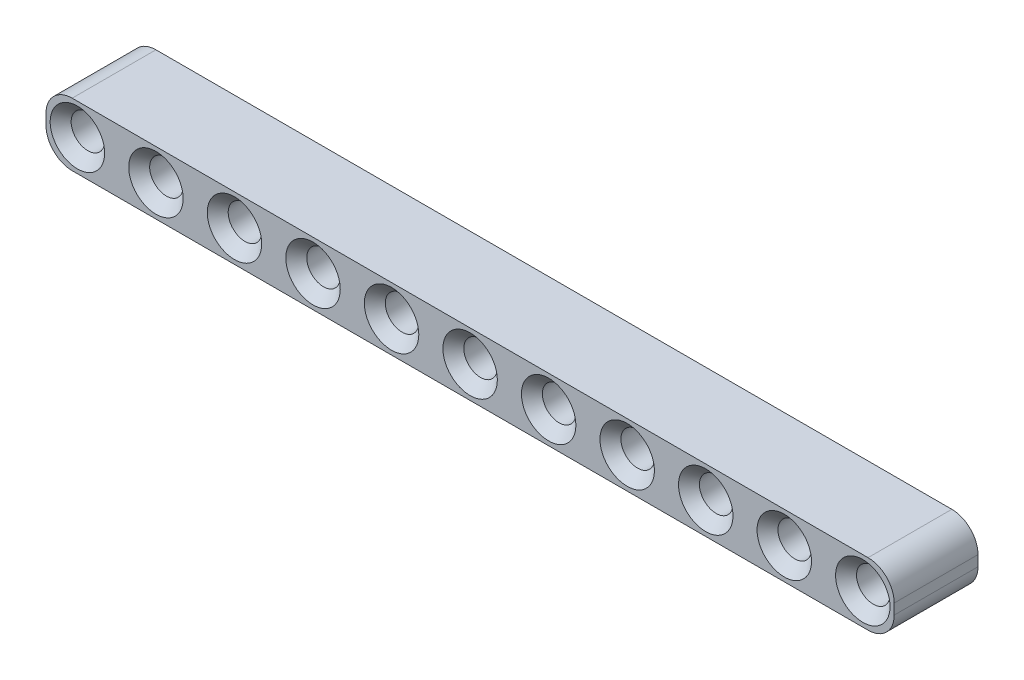
SolidWorks part; units mm, degrees
ref_plane "Front Plane" through (0, 0, 0) normal (0, 0, 1) x (1, 0, 0)
ref_plane "Top Plane" through (0, 0, 0) normal (0, 1, 0) x (1, 0, 0)
ref_plane "Right Plane" through (0, 0, 0) normal (1, 0, 0) x (0, 0, -1)
sketch "Sketch1" plane through (0, 0, 0) normal (0, 0, 1) x (1, 0, 0)
  line L1 (-0.5, 3) -> (75.5, 3)
  line L2 (-3, 0.5) -> (-3, -0.5)
  line L3 (-0.5, -3) -> (75.5, -3)
  line L4 (78, 0.5) -> (78, -0.5)
  circle A0 centre (0, 0) radius 1.6
  arc A1 (75.5, -3) -> (78, -0.5) centre (75.5, -0.5) ccw
  arc A2 (75.5, 3) -> (78, 0.5) centre (75.5, 0.5) cw
  arc A3 (-3, -0.5) -> (-0.5, -3) centre (-0.5, -0.5) ccw
  arc A4 (-0.5, 3) -> (-3, 0.5) centre (-0.5, 0.5) ccw
  circle A5 centre (7.5, 0) radius 1.6
  circle A6 centre (15, 0) radius 1.6
  circle A7 centre (22.5, 0) radius 1.6
  circle A8 centre (30, 0) radius 1.6
  circle A9 centre (37.5, 0) radius 1.6
  circle A10 centre (45, 0) radius 1.6
  circle A11 centre (52.5, 0) radius 1.6
  circle A12 centre (60, 0) radius 1.6
  circle A13 centre (67.5, 0) radius 1.6
  circle A14 centre (75, 0) radius 1.6
  point P8 (-3, 0)
  point P14 (-3, -3)
  point P17 (-3, 3)
  dimension "D1" = 3.2
  dimension "D4" = 2.5
  dimension "D2" = 6
  dimension "D3" = 3
  dimension "D6" = 7.5
  dimension "D5" = 11
extrude "Boss-Extrude1" add sketch "Sketch1" along normal blind 8
chamfer "Chamfer1" distance 1 angle 45 22 edges at (76.6, 0, 0) (76.6, 0, 8) (69.1, 0, 0) (69.1, 0, 8) (61.6, 0, 0) (61.6, 0, 8) (54.1, 0, 0) (54.1, 0, 8) (46.6, 0, 0) (46.6, 0, 8) (39.1, 0, 0) (39.1, 0, 8) (31.6, 0, 0) (31.6, 0, 8) (24.1, 0, 0) (24.1, 0, 8) (16.6, 0, 0) (16.6, 0, 8) (9.1, 0, 0) (9.1, 0, 8) (1.6, 0, 0) (1.6, 0, 8)
